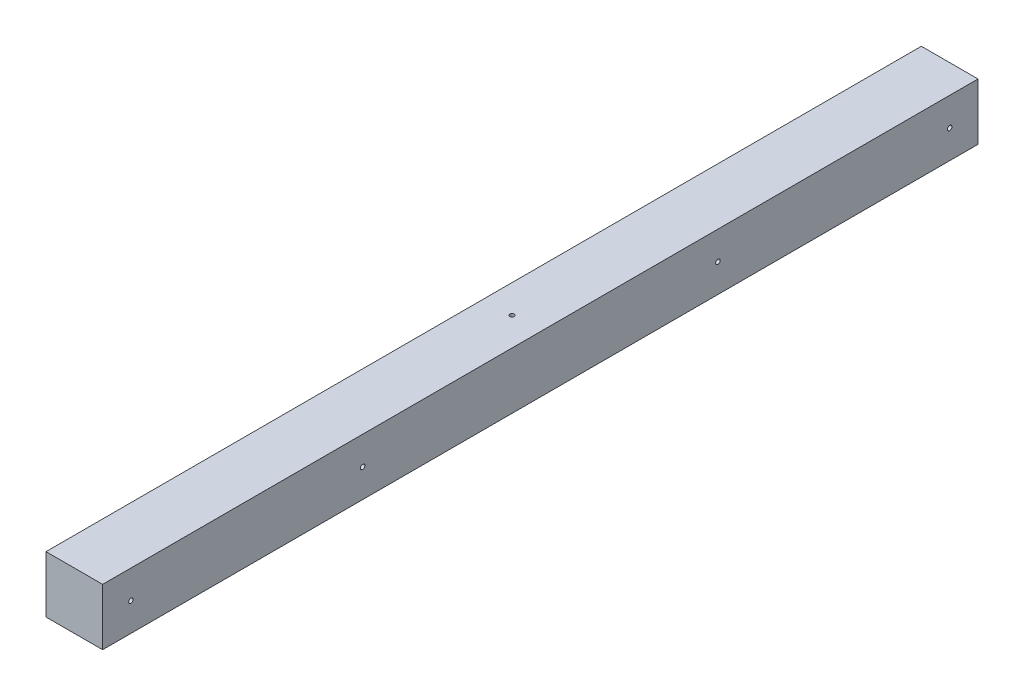
SolidWorks part; units mm, degrees
material "Pin"
ref_plane "Plan de face" through (0, 0, 0) normal (0, 0, 1) x (1, 0, 0)
ref_plane "Plan de dessus" through (0, 0, 0) normal (0, 1, 0) x (1, 0, 0)
ref_plane "Plan de droite" through (0, 0, 0) normal (1, 0, 0) x (0, 0, -1)
sketch "Esquisse1" plane through (0, 0, 0) normal (0, 0, 1) x (1, 0, 0)
  line L1 (22, 22) -> (-22, 22)
  line L2 (22, 22) -> (22, -22)
  line L3 (22, -22) -> (-22, -22)
  line L4 (-22, 22) -> (-22, -22)
  line L5 (22, 22) -> (-22, -22) construction
  line L6 (22, -22) -> (-22, 22) construction
  point P0 (0, 0)
extrude "Boss.-Extru.1" add sketch "Esquisse1" along normal blind 680
sketch "Esquisse2" plane through (-22, 0, 0) normal (1, 0, 0) x (0, -1, 0)
  line L1 (-22, -680) -> (-22, 0) construction
  line L3 (-22, 0) -> (22, 0) construction
  line L4 (-22, -340) -> (22, -340) construction
  line L5 (22, -680) -> (22, 0) construction
  line L6 (22, -680) -> (22, 0) construction
  line L7 (22, 0) -> (-22, 0) construction
  circle A0 centre (0, -22) radius 1.75
  circle A2 centre (0, -658) radius 1.75
  circle A3 centre (0, -202) radius 1.75
  circle A4 centre (0, -478) radius 1.75
  dimension "D1" = 22
  dimension "D2" = 22
  dimension "D3" = 3.5
  dimension "D4" = 3.5
  dimension "D5" = 22
  dimension "D6" = 202
extrude "Enlèv. mat.-Extru.1" cut sketch "Esquisse2" along normal up to surface (44 mm away) up to face at (22, 0, 340)
sketch "Esquisse3" plane through (0, -22, 0) normal (0, -1, 0) x (1, 0, 0)
  circle A0 centre (0, 340) radius 1.75
  dimension "D1" = 3.5
extrude "Enlèv. mat.-Extru.2" cut sketch "Esquisse3" against normal blind 60
